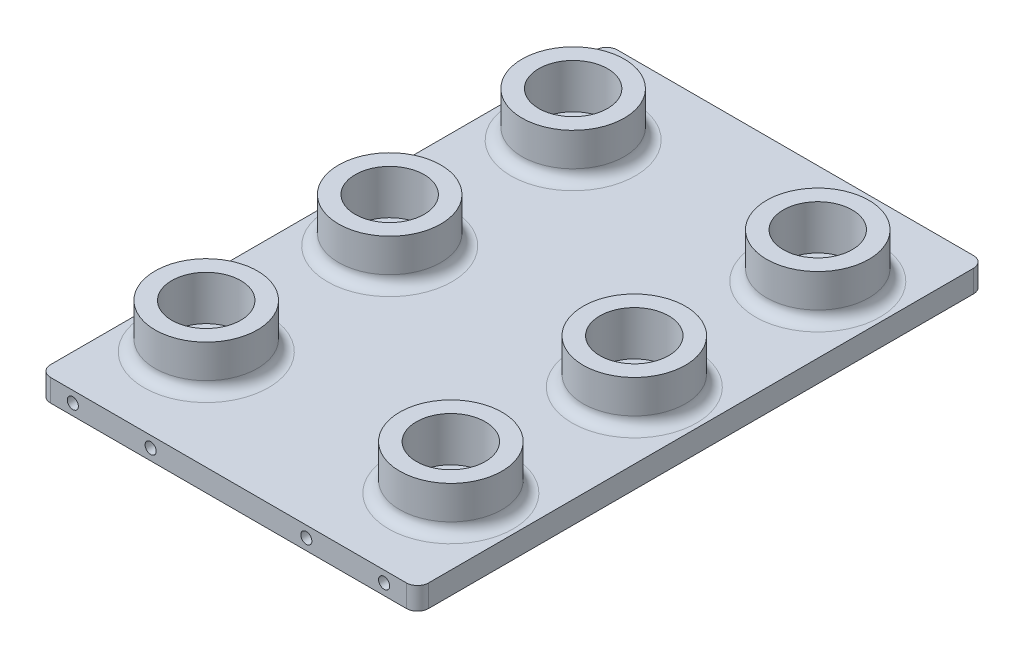
SolidWorks part; units mm, degrees
ref_plane "Front Plane" through (0, 0, 0) normal (0, 0, 1) x (1, 0, 0)
ref_plane "Top Plane" through (0, 0, 0) normal (0, 1, 0) x (1, 0, 0)
ref_plane "Right Plane" through (0, 0, 0) normal (1, 0, 0) x (0, 0, -1)
sketch "Sketch1" plane through (0, 0, 0) normal (0, 1, 0) x (1, 0, 0)
  line L1 (-21.59, 32.385) -> (21.59, 32.385)
  line L2 (-21.59, 32.385) -> (-21.59, -32.385)
  line L3 (-21.59, -32.385) -> (21.59, -32.385)
  line L4 (21.59, 32.385) -> (21.59, -32.385)
  line L5 (-21.59, 32.385) -> (21.59, -32.385) construction
  line L6 (-21.59, -32.385) -> (21.59, 32.385) construction
  point P0 (0, 0)
  dimension "D1" = 43.18
  dimension "D2" = 64.77
extrude "Boss-Extrude1" add sketch "Sketch1" along normal blind 2.54
sketch "Sketch2" plane through (0, 2.54, 0) normal (0, 1, 0) x (1, 0, 0)
  line L0 (-21.59, -32.385) -> (21.59, -32.385) construction
  line L1 (-25.4, -32.385) -> (25.4, -32.385)
  ellipse E0 centre (0, -32.385) end of major axis (0, 18.415) minor radius 25.4 (25.4, -32.385) -> (-25.4, -32.385) ccw
  dimension "D1" = 50.8
  dimension "D2" = 50.8
extrude "Cut-Extrude1" [suppressed] cut sketch "Sketch2" against normal through all
fillet "Fillet1" [suppressed] radius 5.08
sketch "Sketch3" plane through (0, 0, 32.385) normal (0, 0, 1) x (1, 0, 0)
  line L0 (-21.59, 1.27) -> (21.59, 1.27) construction
  line L1 (-21.59, 2.54) -> (-21.59, 0) construction
  line L2 (21.59, 2.54) -> (21.59, 0) construction
  line L3 (8.89, 1.27) -> (-8.89, 1.27) construction
  line L4 (0, 2.54) -> (0, 0) construction
  line L5 (-21.59, 2.54) -> (21.59, 2.54) construction
  circle A0 centre (-17.78, 1.27) radius 0.635
  circle A1 centre (-8.89, 1.27) radius 0.635
  circle A2 centre (8.89, 1.27) radius 0.635
  circle A3 centre (17.78, 1.27) radius 0.635
  dimension "D1" = 17.78
  dimension "D2" = 8.89
  dimension "D3" = 8.89
  dimension "D4" = 1.27
extrude "Cut-Extrude2" cut sketch "Sketch3" against normal blind 2.54
mirror "Mirror1" about plane through (0, 0, 0) normal (0, 0, 1) of "Cut-Extrude2"
sketch "Sketch5" plane through (0, 2.54, 0) normal (0, 1, 0) x (1, 0, 0)
  line L0 (-21.59, 32.385) -> (21.59, -32.385) construction
  line L1 (-13.97, 20.955) -> (13.97, 20.955) construction
  line L2 (-13.97, 20.955) -> (-13.97, -20.955) construction
  line L3 (-13.97, -20.955) -> (13.97, -20.955) construction
  line L4 (13.97, 20.955) -> (13.97, -20.955) construction
  line L5 (-13.97, 20.955) -> (13.97, -20.955) construction
  line L6 (-13.97, -20.955) -> (13.97, 20.955) construction
  line L7 (21.59, 32.385) -> (-21.59, -32.385) construction
  line L8 (-21.59, 32.385) -> (-21.59, -32.385) construction
  circle A0 centre (0, 0) radius 3.937 construction
  circle A1 centre (13.97, 20.955) radius 3.937
  circle A2 centre (13.97, -20.955) radius 3.937
  circle A3 centre (-13.97, -20.955) radius 3.937
  circle A4 centre (-13.97, 20.955) radius 3.937
  circle A5 centre (0, 0) radius 5.842 construction
  circle A6 centre (13.97, 20.955) radius 5.842
  circle A7 centre (-13.97, 20.955) radius 5.842
  circle A8 centre (13.97, -20.955) radius 5.842
  circle A9 centre (-13.97, -20.955) radius 5.842
  circle A10 centre (-13.97, 0) radius 3.937
  circle A11 centre (-13.97, 0) radius 5.842
  circle A12 centre (13.97, 0) radius 3.937
  circle A13 centre (13.97, 0) radius 5.842
  point P0 (0, 0)
  dimension "D3" = 7.874
  dimension "D1" = 7.62
  dimension "D2" = 1.905
extrude "Boss-Extrude3" add sketch "Sketch5" along normal blind 5.08
fillet "Fillet2" radius 1.27 10 edges at (21.59, 1.27, -32.385) (21.59, 1.27, 32.385) (-21.59, 1.27, 32.385) (-21.59, 1.27, -32.385) (13.97, 2.54, 26.797) (13.97, 2.54, -15.113) (-13.97, 2.54, -15.113) (-13.97, 2.54, 26.797) (13.97, 2.54, 5.842) (-13.97, 2.54, 5.842)
